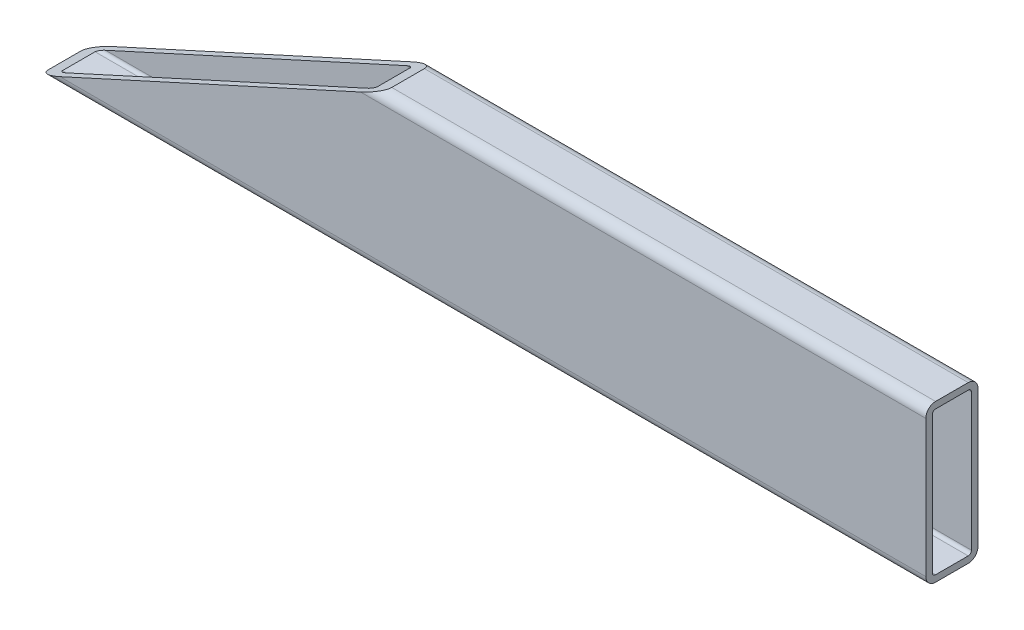
SolidWorks part; units mm, degrees
material "Plain Carbon Steel"
ref_plane "Front Plane" through (0, 0, 0) normal (0, 0, 1) x (1, 0, 0)
ref_plane "Top Plane" through (0, 0, 0) normal (0, 1, 0) x (1, 0, 0)
ref_plane "Right Plane" through (0, 0, 0) normal (1, 0, 0) x (0, 0, -1)
sketch "Sketch1" plane through (0, 0, 0) normal (0, 1, 0) x (1, 0, 0)
  line L0 (215.9, 0) -> (-215.9, 0)
  point P4 (0, 0)
  dimension "D1" = 431.8
other "Rectangular tube 3 X 2 X 0.25(1)"
ref_plane "Plane1" through (215.9, 0, 0) normal (-1, 0, 0) x (0, 0, 1)
sketch "Sketch13" plane through (215.9, 0, 0) normal (-1, 0, 0) x (0, 0, 1)
  line L0 (-7.9375, -34.925) -> (7.9375, -34.925)
  line L1 (-9.525, -33.3375) -> (-9.525, 33.3375)
  line L2 (7.9375, 34.925) -> (-7.9375, 34.925)
  line L3 (9.525, 33.3375) -> (9.525, -33.3375)
  line L4 (-7.9375, -38.1) -> (7.9375, -38.1)
  line L5 (-12.7, -33.3375) -> (-12.7, 33.3375)
  line L6 (7.9375, 38.1) -> (-7.9375, 38.1)
  line L7 (12.7, 33.3375) -> (12.7, -33.3375)
  line L8 (0, 0) -> (12.7, 0) construction
  line L9 (0, 0) -> (0, 38.1) construction
  arc A0 (12.7, 33.3375) -> (7.9375, 38.1) centre (7.9375, 33.3375) ccw
  arc A1 (7.9375, -38.1) -> (12.7, -33.3375) centre (7.9375, -33.3375) ccw
  arc A2 (-12.7, -33.3375) -> (-7.9375, -38.1) centre (-7.9375, -33.3375) ccw
  arc A3 (-7.9375, 38.1) -> (-12.7, 33.3375) centre (-7.9375, 33.3375) ccw
  arc A4 (-7.9375, 34.925) -> (-9.525, 33.3375) centre (-7.9375, 33.3375) ccw
  arc A5 (9.525, 33.3375) -> (7.9375, 34.925) centre (7.9375, 33.3375) ccw
  arc A6 (7.9375, -34.925) -> (9.525, -33.3375) centre (7.9375, -33.3375) ccw
  arc A7 (-9.525, -33.3375) -> (-7.9375, -34.925) centre (-7.9375, -33.3375) ccw
  point P3 (0, -38.1)
  point P4 (-12.7, 0)
  point P5 (0, 0)
  point P6 (12.7, -38.1)
  point P7 (-12.7, -38.1)
  point P8 (-12.7, 38.1)
  point P33 (0, 0)
  point P35 (12.7, 38.1)
  point P36 (12.7, 0)
  point P37 (0, 38.1)
  dimension "D1" = 4.7625
  dimension "Thickness" = 3.175
  dimension "V_leg" = 76.2
  dimension "H_leg" = 25.4
sketch "s" plane through (0, 0, 12.7) normal (0, 0, 1) x (1, 0, 0)
  line L0 (-215.9, -38.1) -> (-215.9, 38.1)
  line L3 (-215.9, 38.1) -> (-48.6944, 38.1)
  line L4 (-48.6944, 38.1) -> (-215.9, -38.1)
  line L15 (-215.9, -33.3375) -> (-215.9, -38.1) construction
  line L16 (-215.9, 38.1) -> (215.9, 38.1) construction
  dimension "D1" = 65.5
extrude "Cut-Extrude1" cut sketch "s" against normal through all
